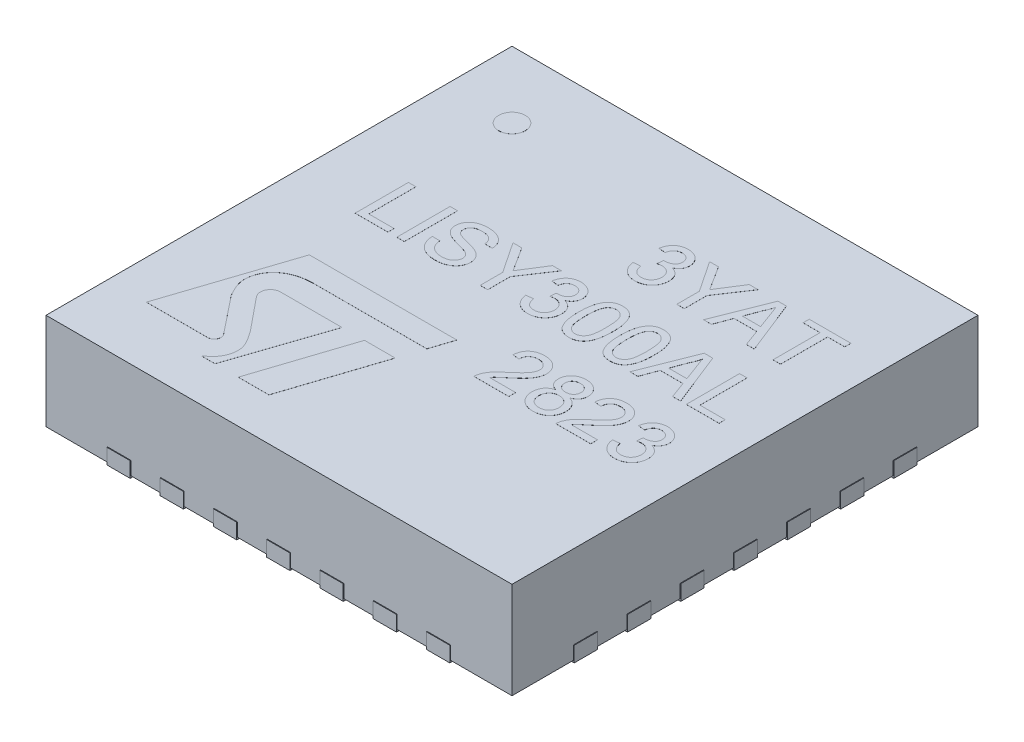
SolidWorks part; units mm, degrees
material "ABS"
ref_plane "Спереди" through (0, 0, 0) normal (0, 0, 1) x (1, 0, 0)
ref_plane "Сверху" through (0, 0, 0) normal (0, 1, 0) x (1, 0, 0)
ref_plane "Справа" through (0, 0, 0) normal (1, 0, 0) x (0, 0, -1)
ref_plane "Плоскость1" through (0, 0.03, 0) normal (0, 1, 0) x (-1, 0, 0)
sketch "Эскиз1" plane through (0, 0.03, 0) normal (0, 1, 0) x (-1, 0, 0)
  line L1 (-3.5, 3.5) -> (3.5, 3.5)
  line L2 (-3.5, 3.5) -> (-3.5, -3.5)
  line L3 (-3.5, -3.5) -> (3.5, -3.5)
  line L4 (3.5, 3.5) -> (3.5, -3.5)
  dimension "D1" = 7
  dimension "D2" = 3.5
  dimension "D3" = 3.5
  dimension "D4" = 7
extrude "Вытянуть1" add sketch "Эскиз1" along normal blind 1.45
sketch "Эскиз2" plane through (0, 1.48, 0) normal (0, 1, 0) x (1, 0, 0)
  line L11 (-0.0907, -0.7374) -> (-0.2022, -1.0765)
  line L17 (-2.3073, -0.7374) -> (-0.0907, -0.7374)
  line L18 (-1.8216, -1.0765) -> (-0.2022, -1.0765)
  line L19 (-1.2498, -2.8618) -> (-0.7806, -1.4346)
  line L20 (-0.7806, -1.4346) -> (-0.32, -1.4346)
  line L21 (-2.3706, -1.8465) -> (-1.918, -2.4136)
  line L22 (-2.9159, -2.5759) -> (-2.3073, -0.7374)
  line L23 (-2.9159, -2.5759) -> (-1.9962, -2.5759)
  line L24 (-1.8063, -2.8618) -> (-1.5995, -2.8618)
  line L25 (-1.1177, -1.4366) -> (-1.5995, -2.8618)
  line L26 (-2.152, -1.6885) -> (-1.7541, -2.177)
  line L27 (-1.1177, -1.4366) -> (-2.042, -1.4366)
  line L28 (-0.32, -1.4346) -> (-0.7892, -2.8618)
  line L29 (-1.2498, -2.8618) -> (-0.7892, -2.8618)
  arc A2 (-1.9962, -2.5759) -> (-1.918, -2.4136) centre (-1.9962, -2.4759) ccw
  arc A3 (-2.042, -1.4366) -> (-2.152, -1.6885) centre (-2.042, -1.5866) ccw
  spline S2 degree 3 poles (-1.7541, -2.177) (-1.6776, -2.2839) (-1.5449, -2.4694) (-1.6528, -2.7504) (-1.7663, -2.8328) (-1.8063, -2.8618) knots 0 0 0 0 0.468346 0.812573 1 1 1 1
  spline S3 degree 3 poles (-2.3706, -1.8465) (-2.4194, -1.7566) (-2.5187, -1.5737) (-2.406, -1.225) (-2.1049, -1.0753) (-1.9007, -1.0762) (-1.8216, -1.0765) knots 0 0 0 0 0.244215 0.496481 0.805126 1 1 1 1
  text T0 "         3YAT\r\nLISY300AL\r\n          2823" font "Arial" height 0.8
  dimension "D3" = 0.1
  dimension "D4" = 0.15
extrude "Вытянуть2" add sketch "Эскиз2" along normal blind 0.001
sketch "Эскиз3" plane through (0, 1.48, 0) normal (0, 1, 0) x (1, 0, 0)
  line L0 (3.5, 3.5) -> (-3.5, 3.5) construction
  line L1 (-3.5, 3.5) -> (-3.5, -3.5) construction
  circle A0 centre (-2.5, 2.5) radius 0.2
  dimension "D1" = 1
  dimension "D2" = 1
extrude "Вытянуть3" add sketch "Эскиз3" along normal blind 0.001
sketch "Эскиз4" plane through (0, 0.03, 0) normal (0, -1, 0) x (1, 0, 0)
  line L0 (-2.225, 3.51) -> (-2.575, 3.51)
  line L1 (-1.425, 3.51) -> (-1.775, 3.51)
  line L2 (-1.425, 3.51) -> (-1.425, 3.05)
  line L3 (-1.425, 3.05) -> (-1.775, 3.05)
  line L4 (-1.775, 3.51) -> (-1.775, 3.05)
  line L5 (-2.225, 3.51) -> (-2.225, 3.05)
  line L6 (-2.225, 3.05) -> (-2.575, 3.05)
  line L7 (-2.575, 3.51) -> (-2.575, 3.05)
  line L8 (-0.625, 3.51) -> (-0.975, 3.51)
  line L9 (-0.625, 3.51) -> (-0.625, 3.05)
  line L10 (-0.625, 3.05) -> (-0.975, 3.05)
  line L11 (-0.975, 3.51) -> (-0.975, 3.05)
  line L12 (0.175, 3.51) -> (-0.175, 3.51)
  line L13 (0.175, 3.51) -> (0.175, 3.05)
  line L14 (0.175, 3.05) -> (-0.175, 3.05)
  line L15 (-0.175, 3.51) -> (-0.175, 3.05)
  line L16 (0.975, 3.51) -> (0.625, 3.51)
  line L17 (0.975, 3.51) -> (0.975, 3.05)
  line L18 (0.975, 3.05) -> (0.625, 3.05)
  line L19 (0.625, 3.51) -> (0.625, 3.05)
  line L20 (1.775, 3.51) -> (1.425, 3.51)
  line L21 (1.775, 3.51) -> (1.775, 3.05)
  line L22 (1.775, 3.05) -> (1.425, 3.05)
  line L23 (1.425, 3.51) -> (1.425, 3.05)
  line L24 (2.575, 3.51) -> (2.225, 3.51)
  line L25 (2.575, 3.51) -> (2.575, 3.05)
  line L26 (2.575, 3.05) -> (2.225, 3.05)
  line L27 (2.225, 3.51) -> (2.225, 3.05)
  line L28 (3.51, 2.225) -> (3.51, 2.575)
  line L29 (3.51, 1.425) -> (3.51, 1.775)
  line L30 (3.51, 1.425) -> (3.05, 1.425)
  line L31 (3.05, 1.425) -> (3.05, 1.775)
  line L32 (3.51, 1.775) -> (3.05, 1.775)
  line L33 (3.51, 2.225) -> (3.05, 2.225)
  line L34 (3.05, 2.225) -> (3.05, 2.575)
  line L35 (3.51, 2.575) -> (3.05, 2.575)
  line L36 (3.51, 0.625) -> (3.51, 0.975)
  line L37 (3.51, 0.625) -> (3.05, 0.625)
  line L38 (3.05, 0.625) -> (3.05, 0.975)
  line L39 (3.51, 0.975) -> (3.05, 0.975)
  line L40 (3.51, -0.175) -> (3.51, 0.175)
  line L41 (3.51, -0.175) -> (3.05, -0.175)
  line L42 (3.05, -0.175) -> (3.05, 0.175)
  line L43 (3.51, 0.175) -> (3.05, 0.175)
  line L44 (3.51, -0.975) -> (3.51, -0.625)
  line L45 (3.51, -0.975) -> (3.05, -0.975)
  line L46 (3.05, -0.975) -> (3.05, -0.625)
  line L47 (3.51, -0.625) -> (3.05, -0.625)
  line L48 (3.51, -1.775) -> (3.51, -1.425)
  line L49 (3.51, -1.775) -> (3.05, -1.775)
  line L50 (3.05, -1.775) -> (3.05, -1.425)
  line L51 (3.51, -1.425) -> (3.05, -1.425)
  line L52 (3.51, -2.575) -> (3.51, -2.225)
  line L53 (3.51, -2.575) -> (3.05, -2.575)
  line L54 (3.05, -2.575) -> (3.05, -2.225)
  line L55 (3.51, -2.225) -> (3.05, -2.225)
  line L56 (2.225, -3.51) -> (2.575, -3.51)
  line L57 (1.425, -3.51) -> (1.775, -3.51)
  line L58 (1.425, -3.51) -> (1.425, -3.05)
  line L59 (1.425, -3.05) -> (1.775, -3.05)
  line L60 (1.775, -3.51) -> (1.775, -3.05)
  line L61 (2.225, -3.51) -> (2.225, -3.05)
  line L62 (2.225, -3.05) -> (2.575, -3.05)
  line L63 (2.575, -3.51) -> (2.575, -3.05)
  line L64 (0.625, -3.51) -> (0.975, -3.51)
  line L65 (0.625, -3.51) -> (0.625, -3.05)
  line L66 (0.625, -3.05) -> (0.975, -3.05)
  line L67 (0.975, -3.51) -> (0.975, -3.05)
  line L68 (-0.175, -3.51) -> (0.175, -3.51)
  line L69 (-0.175, -3.51) -> (-0.175, -3.05)
  line L70 (-0.175, -3.05) -> (0.175, -3.05)
  line L71 (0.175, -3.51) -> (0.175, -3.05)
  line L72 (-0.975, -3.51) -> (-0.625, -3.51)
  line L73 (-0.975, -3.51) -> (-0.975, -3.05)
  line L74 (-0.975, -3.05) -> (-0.625, -3.05)
  line L75 (-0.625, -3.51) -> (-0.625, -3.05)
  line L76 (-1.775, -3.51) -> (-1.425, -3.51)
  line L77 (-1.775, -3.51) -> (-1.775, -3.05)
  line L78 (-1.775, -3.05) -> (-1.425, -3.05)
  line L79 (-1.425, -3.51) -> (-1.425, -3.05)
  line L80 (-2.575, -3.51) -> (-2.225, -3.51)
  line L81 (-2.575, -3.51) -> (-2.575, -3.05)
  line L82 (-2.575, -3.05) -> (-2.225, -3.05)
  line L83 (-2.225, -3.51) -> (-2.225, -3.05)
  line L84 (-3.51, -2.225) -> (-3.51, -2.575)
  line L85 (-3.51, -1.425) -> (-3.51, -1.775)
  line L86 (-3.51, -1.425) -> (-3.05, -1.425)
  line L87 (-3.05, -1.425) -> (-3.05, -1.775)
  line L88 (-3.51, -1.775) -> (-3.05, -1.775)
  line L89 (-3.51, -2.225) -> (-3.05, -2.225)
  line L90 (-3.05, -2.225) -> (-3.05, -2.575)
  line L91 (-3.51, -2.575) -> (-3.05, -2.575)
  line L92 (-3.51, -0.625) -> (-3.51, -0.975)
  line L93 (-3.51, -0.625) -> (-3.05, -0.625)
  line L94 (-3.05, -0.625) -> (-3.05, -0.975)
  line L95 (-3.51, -0.975) -> (-3.05, -0.975)
  line L96 (-3.51, 0.175) -> (-3.51, -0.175)
  line L97 (-3.51, 0.175) -> (-3.05, 0.175)
  line L98 (-3.05, 0.175) -> (-3.05, -0.175)
  line L99 (-3.51, -0.175) -> (-3.05, -0.175)
  line L100 (-3.51, 0.975) -> (-3.51, 0.625)
  line L101 (-3.51, 0.975) -> (-3.05, 0.975)
  line L102 (-3.05, 0.975) -> (-3.05, 0.625)
  line L103 (-3.51, 0.625) -> (-3.05, 0.625)
  line L104 (-3.51, 1.775) -> (-3.51, 1.425)
  line L105 (-3.51, 1.775) -> (-3.05, 1.775)
  line L106 (-3.05, 1.775) -> (-3.05, 1.425)
  line L107 (-3.51, 1.425) -> (-3.05, 1.425)
  line L108 (-3.51, 2.575) -> (-3.51, 2.225)
  line L109 (-3.51, 2.575) -> (-3.05, 2.575)
  line L110 (-3.05, 2.575) -> (-3.05, 2.225)
  line L111 (-3.51, 2.225) -> (-3.05, 2.225)
  dimension "D1" = 0.35
  dimension "D2" = 0.46
  dimension "D3" = 3.51
  dimension "D4" = 2.225
extrude "Вытянуть4" add sketch "Эскиз4" along normal blind 0.03 and the other way blind 0.2
